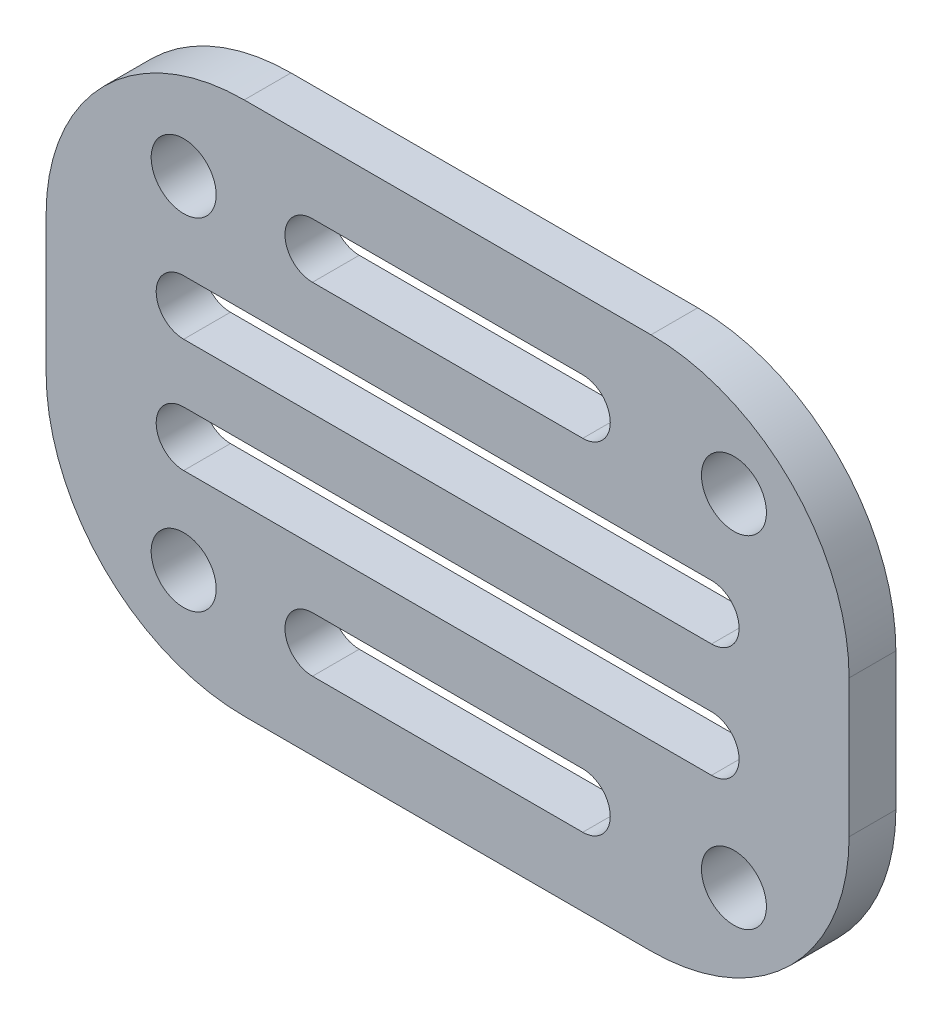
SolidWorks part; units mm, degrees
ref_plane "Front Plane" through (0, 0, 0) normal (0, 0, 1) x (1, 0, 0)
ref_plane "Top Plane" through (0, 0, 0) normal (0, 1, 0) x (1, 0, 0)
ref_plane "Right Plane" through (0, 0, 0) normal (1, 0, 0) x (0, 0, -1)
sketch "Sketch1" plane through (0, 0, 0) normal (0, 0, 1) x (1, 0, 0)
  line L0 (-12.7, -7.874) -> (12.7, -7.874) construction
  line L5 (15.338, -9.6408) -> (12.7, -7.874) construction
  line L6 (-9.906, 12.319) -> (8.8722, 12.319)
  line L7 (12.7, -7.874) -> (12.7, 7.874) construction
  line L8 (12.7, 7.874) -> (-12.7, 7.874) construction
  line L9 (-12.7, 7.874) -> (-12.7, -7.874) construction
  line L10 (-19.05, 3.175) -> (-19.05, -3.175)
  line L11 (-9.906, -12.319) -> (8.8722, -12.319)
  line L12 (18.0162, 3.175) -> (18.0162, -3.175)
  line L15 (6.9386, 0) -> (-6.9386, 0) construction
  circle A0 centre (-12.7, 7.874) radius 1.5
  circle A1 centre (-12.7, -7.874) radius 1.5
  circle A2 centre (12.7, 7.874) radius 1.5
  circle A3 centre (12.7, -7.874) radius 1.5
  arc A4 (8.8722, -12.319) -> (18.0162, -3.175) centre (8.8722, -3.175) ccw
  arc A5 (8.8722, 12.319) -> (18.0162, 3.175) centre (8.8722, 3.175) cw
  arc A6 (-9.906, 12.319) -> (-19.05, 3.175) centre (-9.906, 3.175) ccw
  arc A7 (-19.05, -3.175) -> (-9.906, -12.319) centre (-9.906, -3.175) ccw
  point P0 (0, 0)
  point P2 (-12.7, 0)
  point P3 (0, 0)
  dimension "D1" = 3
  dimension "D6" = 6.35
  dimension "D7" = 3.175
  dimension "D2" = 15.748
  dimension "D3" = 12.7
  dimension "D4" = 4.445
  dimension "D5" = 6.35
  dimension "D9" = 12.7
extrude "Boss-Extrude1" add sketch "Sketch1" along normal blind 2.159
sketch "Sketch4" plane through (0, 0, 2.159) normal (0, 0, 1) x (1, 0, 0)
  line L1 (-6.755, 7.874) -> (5.7212, 7.874) construction
  line L2 (-6.755, 9.144) -> (5.7212, 9.144)
  line L3 (-6.755, 6.604) -> (5.7212, 6.604)
  line L4 (-12.7, 2.6247) -> (11.6662, 2.6247) construction
  line L5 (-12.7, 3.8947) -> (11.6662, 3.8947)
  line L6 (-12.7, 1.3547) -> (11.6662, 1.3547)
  line L7 (-12.7, -2.6247) -> (11.6662, -2.6247) construction
  line L8 (-12.7, -1.3547) -> (11.6662, -1.3547)
  line L9 (-12.7, -3.8947) -> (11.6662, -3.8947)
  line L10 (-6.755, -7.874) -> (5.7212, -7.874) construction
  line L11 (-6.755, -6.604) -> (5.7212, -6.604)
  line L12 (-6.755, -9.144) -> (5.7212, -9.144)
  line L13 (-0.5169, 6.604) -> (-0.5169, 3.8947) construction
  line L14 (-0.5169, 1.3547) -> (-0.5169, -1.3547) construction
  line L15 (-0.5169, -3.8947) -> (-0.5169, -6.604) construction
  line L16 (-9.906, 12.319) -> (8.8722, 12.319) construction
  line L17 (-8.025, 7.874) -> (-11.2, 7.874) construction
  line L18 (18.0162, 3.175) -> (18.0162, -3.175) construction
  line L19 (-12.7, 7.874) -> (-12.7, 2.6247) construction
  arc A3 (-6.755, 9.144) -> (-6.755, 6.604) centre (-6.755, 7.874) ccw
  arc A4 (5.7212, 6.604) -> (5.7212, 9.144) centre (5.7212, 7.874) ccw
  arc A5 (-12.7, 3.8947) -> (-12.7, 1.3547) centre (-12.7, 2.6247) ccw
  arc A6 (11.6662, 1.3547) -> (11.6662, 3.8947) centre (11.6662, 2.6247) ccw
  arc A7 (-12.7, -1.3547) -> (-12.7, -3.8947) centre (-12.7, -2.6247) ccw
  arc A8 (11.6662, -3.8947) -> (11.6662, -1.3547) centre (11.6662, -2.6247) ccw
  arc A9 (-6.755, -6.604) -> (-6.755, -9.144) centre (-6.755, -7.874) ccw
  arc A10 (5.7212, -9.144) -> (5.7212, -6.604) centre (5.7212, -7.874) ccw
  circle A13 centre (-12.7, 7.874) radius 1.5 construction
  point P4 (-0.5169, 7.874)
  point P9 (-0.5169, 2.6247)
  point P16 (-0.5169, -2.6247)
  point P23 (-0.5169, -7.874)
  point P40 (-0.5169, 12.319)
  point P49 (-0.5169, 0)
  point P52 (18.0162, 0)
  dimension "D2" = 1.27
  dimension "D3" = 3.175
  dimension "D1" = 3.175
extrude "Cut-Extrude1" cut sketch "Sketch4" against normal through all
